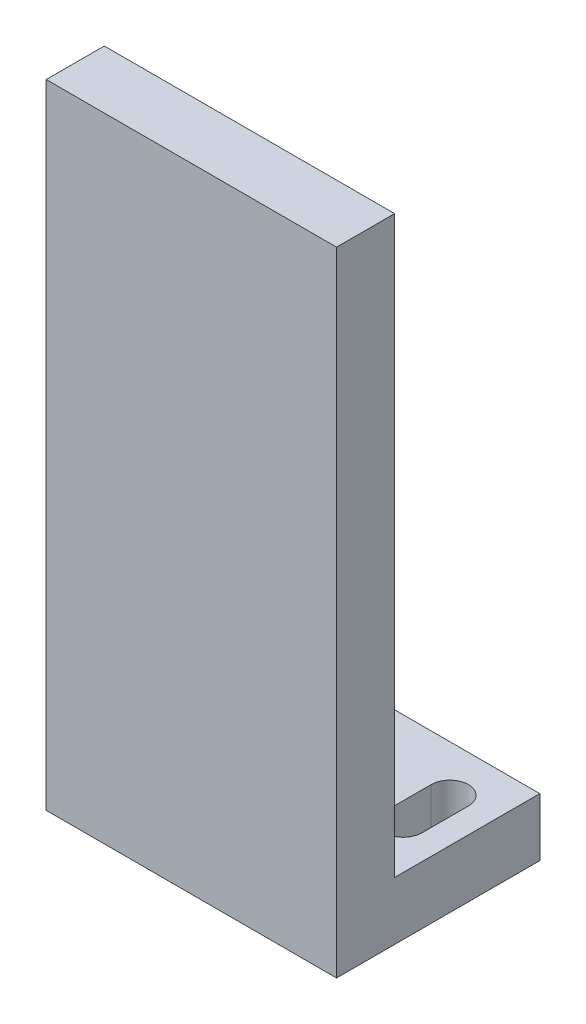
SolidWorks part; units mm, degrees
ref_plane "前视基准面" through (0, 0, 0) normal (0, 0, 1) x (1, 0, 0)
ref_plane "上视基准面" through (0, 0, 0) normal (0, 1, 0) x (1, 0, 0)
ref_plane "右视基准面" through (0, 0, 0) normal (1, 0, 0) x (0, 0, -1)
sketch "草图1" plane through (0, 0, 0) normal (0, 1, 0) x (1, 0, 0)
  line L1 (25, -17.5) -> (-25, -17.5)
  line L2 (25, -17.5) -> (25, 17.5)
  line L3 (25, 17.5) -> (-25, 17.5)
  line L4 (-25, -17.5) -> (-25, 17.5)
  line L5 (25, -17.5) -> (-25, 17.5) construction
  line L6 (25, 17.5) -> (-25, -17.5) construction
  point P0 (0, 0)
  dimension "D1" = 50
  dimension "D2" = 35
extrude "凸台-拉伸1" add sketch "草图1" along normal blind 109
sketch "草图2" plane through (0, 109, 0) normal (0, 1, 0) x (1, 0, 0)
  line L0 (25, -17.5) -> (25, 17.5) construction
  line L1 (-25, 17.5) -> (25, 17.5)
  line L2 (-25, 17.5) -> (-25, -7.5)
  line L3 (-25, -7.5) -> (25, -7.5)
  line L4 (25, 17.5) -> (25, -7.5)
  line L5 (-25, -17.5) -> (25, -17.5) construction
  dimension "D1" = 10
extrude "切除-拉伸1" cut sketch "草图2" against normal offset from surface (99 mm away) 10 up to face at (0, 0, 0)
sketch "草图3" plane through (0, 10, 0) normal (0, 1, 0) x (1, 0, 0)
  line L0 (0, 17.5) -> (0, 5.5) construction
  line L1 (-25, 17.5) -> (25, 17.5) construction
  line L2 (0, 5.5) -> (-17.5, 5.5) construction
  line L3 (-17.5, 1.5) -> (-17.5, 9.5) construction
  line L4 (-20.7, 1.5) -> (-20.7, 9.5)
  line L5 (-14.3, 1.5) -> (-14.3, 9.5)
  line L6 (17.5, 1.5) -> (17.5, 9.5) construction
  line L7 (20.7, 1.5) -> (20.7, 9.5)
  line L8 (14.3, 1.5) -> (14.3, 9.5)
  arc A0 (-20.7, 1.5) -> (-14.3, 1.5) centre (-17.5, 1.5) ccw
  arc A1 (-14.3, 9.5) -> (-20.7, 9.5) centre (-17.5, 9.5) ccw
  arc A2 (20.7, 1.5) -> (14.3, 1.5) centre (17.5, 1.5) cw
  arc A3 (14.3, 9.5) -> (20.7, 9.5) centre (17.5, 9.5) cw
  point P8 (-17.5, 5.5)
  point P15 (17.5, 5.5)
  dimension "D2" = 3.2
  dimension "D1" = 35
  dimension "D3" = 8
  dimension "D4" = 12
extrude "切除-拉伸2" cut sketch "草图3" against normal through all
sketch "草图4" plane through (0, 0, 7.5) normal (0, 0, -1) x (-1, 0, 0)
  line L0 (0, 109) -> (0, 69) construction
  line L1 (25, 109) -> (-25, 109) construction
  circle A0 centre (0, 69) radius 4.5949
  circle A1 centre (0, 99) radius 3.3452
  dimension "D1" = 30
  dimension "D2" = 10
